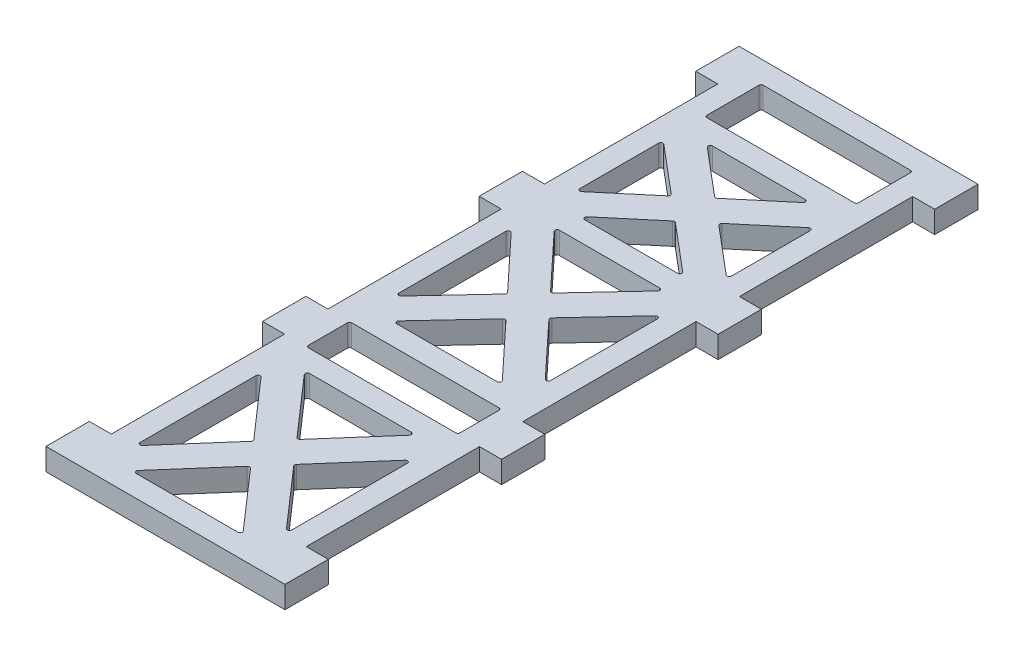
SolidWorks part; units mm, degrees
ref_plane "Front Plane" through (0, 0, 0) normal (0, 0, 1) x (1, 0, 0)
ref_plane "Top Plane" through (0, 0, 0) normal (0, 1, 0) x (1, 0, 0)
ref_plane "Right Plane" through (0, 0, 0) normal (1, 0, 0) x (0, 0, -1)
sketch "Sketch1" plane through (0, 0, 0) normal (0, 1, 0) x (1, 0, 0)
  line L1 (22.5, -80) -> (-22.5, -80)
  line L2 (22.5, -80) -> (22.5, 80)
  line L3 (22.5, 80) -> (-22.5, 80)
  line L4 (-22.5, -80) -> (-22.5, 80)
  line L5 (22.5, -80) -> (-22.5, 80) construction
  line L6 (22.5, 80) -> (-22.5, -80) construction
  point P0 (0, 0)
  dimension "D1" = 45
  dimension "D2" = 160
extrude "Boss-Extrude1" add sketch "Sketch1" along normal blind 5.08
sketch "Sketch2" plane through (0, 5.08, 0) normal (0, 1, 0) x (1, 0, 0)
  line L0 (22.5, 30) -> (27.58, 30)
  line L1 (22.5, 80) -> (27.58, 80)
  line L2 (22.5, 80) -> (22.5, 70)
  line L3 (22.5, 70) -> (27.58, 70)
  line L4 (27.58, 80) -> (27.58, 70)
  line L5 (22.5, 30) -> (22.5, 20)
  line L6 (22.5, 20) -> (27.58, 20)
  line L7 (27.58, 30) -> (27.58, 20)
  line L8 (22.5, -20) -> (27.58, -20)
  line L9 (22.5, -20) -> (22.5, -30)
  line L10 (22.5, -30) -> (27.58, -30)
  line L11 (27.58, -20) -> (27.58, -30)
  line L12 (22.5, -70) -> (27.58, -70)
  line L13 (22.5, -70) -> (22.5, -80)
  line L14 (22.5, -80) -> (27.58, -80)
  line L15 (27.58, -70) -> (27.58, -80)
  line L16 (22.5, -80) -> (22.5, 80) construction
  line L18 (-22.5, -80) -> (22.5, -80) construction
  dimension "D1" = 10
  dimension "D2" = 5.08
  dimension "D3" = 4
extrude "Boss-Extrude2" add sketch "Sketch2" against normal up to surface (5.08 mm away) up to face at (0, 0, 0)
mirror "Mirror1" about plane through (0, 0, 0) normal (1, 0, 0) of "Boss-Extrude2"
sketch "Sketch3" plane through (0, 5.08, 0) normal (0, 1, 0) x (1, 0, 0)
  line L0 (27.58, 80) -> (-27.58, 80) construction
  line L1 (17.5, 62) -> (-17.5, 62)
  line L2 (17.5, 62) -> (17.5, 75)
  line L3 (17.5, 75) -> (-17.5, 75)
  line L4 (-17.5, 62) -> (-17.5, 75)
  line L5 (17.5, 62) -> (-17.5, 75) construction
  line L6 (17.5, 75) -> (-17.5, 62) construction
  line L7 (17.5, 75) -> (22.5, 75) construction
  line L8 (17.5, 75) -> (17.5, 80) construction
  line L9 (17.5, 80) -> (22.5, 80) construction
  line L10 (22.5, 75) -> (22.5, 80) construction
  line L11 (22.5, 30) -> (22.5, 70) construction
  line L12 (-17.5, 27.5) -> (17.5, 57) construction
  line L13 (-17.5, 57) -> (17.5, 57)
  line L14 (-17.5, 57) -> (-17.5, 27.5)
  line L15 (-17.5, 27.5) -> (17.5, 27.5)
  line L16 (17.5, 57) -> (17.5, 27.5)
  line L17 (17.5, 27.5) -> (-17.5, 57) construction
  line L18 (-27.58, -80) -> (27.58, -80) construction
  line L19 (-17.5, 22.5) -> (17.5, 22.5)
  line L20 (-17.5, 22.5) -> (-17.5, -15)
  line L21 (-17.5, -15) -> (17.5, -15)
  line L22 (17.5, 22.5) -> (17.5, -15)
  line L23 (-17.5, -20) -> (17.5, -20)
  line L24 (-17.5, -20) -> (-17.5, -30)
  line L25 (-17.5, -30) -> (17.5, -30)
  line L26 (17.5, -20) -> (17.5, -30)
  line L27 (-17.5, -35) -> (17.5, -35)
  line L28 (-17.5, -35) -> (-17.5, -75)
  line L29 (-17.5, -75) -> (17.5, -75)
  line L30 (17.5, -35) -> (17.5, -75)
  line L31 (-17.5, -75) -> (-22.5, -75) construction
  line L32 (-17.5, -75) -> (-17.5, -80) construction
  line L33 (-17.5, -80) -> (-22.5, -80) construction
  line L34 (-22.5, -75) -> (-22.5, -80) construction
  line L35 (17.5, -75) -> (-17.5, -35) construction
  line L36 (-17.5, -30) -> (17.5, -20) construction
  line L37 (-17.5, -15) -> (17.5, 22.5) construction
  line L38 (17.5, 57) -> (17.5, 62) construction
  line L39 (17.5, 27.5) -> (17.5, 22.5) construction
  line L40 (27.58, -20) -> (22.5, -20) construction
  line L41 (17.5, -30) -> (17.5, -35) construction
  line L42 (-27.58, -25) -> (27.58, -25) construction
  line L43 (-27.58, -30) -> (-27.58, -20) construction
  line L44 (27.58, -30) -> (27.58, -20) construction
  line L45 (27.58, 25) -> (-27.58, 25) construction
  line L46 (27.58, 20) -> (27.58, 30) construction
  line L47 (-27.58, 20) -> (-27.58, 30) construction
  point P0 (0, 68.5)
  point P17 (0, 42.25)
  point P35 (0, 3.75)
  point P36 (0, -55)
  point P37 (0, -25)
  point P52 (17.5, 25)
  dimension "D1" = 5
  dimension "D2" = 13
  dimension "D3" = 5
extrude "Cut-Extrude1" cut sketch "Sketch3" against normal through all
sketch "Sketch4" plane through (0, 5.08, 0) normal (0, 1, 0) x (1, 0, 0)
  line L0 (-17.5, -75) -> (17.5, -35) construction
  line L1 (17.5, -75) -> (-17.5, -35) construction
  line L2 (-17.5, -40.3151) -> (-4.6507, -55)
  line L3 (-17.5, -35) -> (-17.5, -75) construction
  line L4 (-4.6507, -55) -> (-17.5, -69.6849)
  line L5 (-17.5, -69.6849) -> (-17.5, -75)
  line L6 (-17.5, -75) -> (-12.8493, -75)
  line L7 (-17.5, -75) -> (17.5, -75) construction
  line L8 (-12.8493, -75) -> (0, -60.3151)
  line L9 (0, -60.3151) -> (12.8493, -75)
  line L10 (12.8493, -75) -> (17.5, -75)
  line L11 (17.5, -75) -> (17.5, -69.6849)
  line L12 (17.5, -75) -> (17.5, -35) construction
  line L13 (17.5, -69.6849) -> (4.6507, -55)
  line L14 (4.6507, -55) -> (17.5, -40.3151)
  line L15 (17.5, -40.3151) -> (17.5, -35)
  line L16 (17.5, -35) -> (12.8493, -35)
  line L17 (17.5, -35) -> (-17.5, -35) construction
  line L18 (12.8493, -35) -> (0, -49.6849)
  line L19 (0, -49.6849) -> (-12.8493, -35)
  line L20 (-12.8493, -35) -> (-17.5, -35)
  line L21 (-17.5, -35) -> (-17.5, -40.3151)
  line L22 (-17.5, -15) -> (17.5, 22.5) construction
  line L23 (17.5, -15) -> (-17.5, 22.5) construction
  line L24 (-17.5, 27.5) -> (17.5, 57) construction
  line L25 (17.5, 27.5) -> (-17.5, 57) construction
  line L26 (-12.7124, 22.5) -> (0, 8.8796)
  line L27 (17.5, 22.5) -> (-17.5, 22.5) construction
  line L28 (0, 8.8796) -> (12.7124, 22.5)
  line L29 (12.7124, 22.5) -> (17.5, 22.5)
  line L30 (17.5, 22.5) -> (17.5, 17.3704)
  line L31 (17.5, -15) -> (17.5, 22.5) construction
  line L32 (17.5, 17.3704) -> (4.7876, 3.75)
  line L33 (4.7876, 3.75) -> (17.5, -9.8704)
  line L34 (17.5, -9.8704) -> (17.5, -15)
  line L35 (17.5, -15) -> (12.7124, -15)
  line L36 (-17.5, -15) -> (17.5, -15) construction
  line L37 (12.7124, -15) -> (0, -1.3796)
  line L38 (0, -1.3796) -> (-12.7124, -15)
  line L39 (-12.7124, -15) -> (-17.5, -15)
  line L40 (-17.5, -15) -> (-17.5, -9.8704)
  line L41 (-17.5, 22.5) -> (-17.5, -15) construction
  line L42 (-17.5, -9.8704) -> (-4.7876, 3.75)
  line L43 (-4.7876, 3.75) -> (-17.5, 17.3704)
  line L44 (-17.5, 17.3704) -> (-17.5, 22.5)
  line L45 (-17.5, 22.5) -> (-12.7124, 22.5)
  line L46 (-17.5, 52.4226) -> (-5.4308, 42.25)
  line L47 (-17.5, 57) -> (-17.5, 27.5) construction
  line L48 (-5.4308, 42.25) -> (-17.5, 32.0774)
  line L49 (-17.5, 32.0774) -> (-17.5, 27.5)
  line L50 (-17.5, 27.5) -> (-12.0692, 27.5)
  line L51 (-17.5, 27.5) -> (17.5, 27.5) construction
  line L52 (-12.0692, 27.5) -> (0, 37.6726)
  line L53 (0, 37.6726) -> (12.0692, 27.5)
  line L54 (12.0692, 27.5) -> (17.5, 27.5)
  line L55 (17.5, 27.5) -> (17.5, 32.0774)
  line L56 (17.5, 27.5) -> (17.5, 57) construction
  line L57 (17.5, 32.0774) -> (5.4308, 42.25)
  line L58 (5.4308, 42.25) -> (17.5, 52.4226)
  line L59 (17.5, 52.4226) -> (17.5, 57)
  line L60 (17.5, 57) -> (12.0692, 57)
  line L61 (12.0692, 57) -> (0, 46.8274)
  line L62 (0, 46.8274) -> (-12.0692, 57)
  line L63 (17.5, 57) -> (-17.5, 57) construction
  line L64 (-12.0692, 57) -> (-17.5, 57)
  line L65 (-17.5, 57) -> (-17.5, 52.4226)
  point P22 (0, -55)
  point P45 (0, 42.25)
  point P46 (0, 3.75)
  dimension "D1" = 7
  dimension "D2" = 7
  dimension "D3" = 7
extrude "Boss-Extrude3" add sketch "Sketch4" against normal up to surface (5.08 mm away) up to face at (0, 0, 55)
fillet "Fillet1" radius 0.5 44 edges at (17.5, 2.54, -75) (-17.5, 2.54, -75) (-17.5, 2.54, -62) (17.5, 2.54, -62) (17.5, 2.54, 20) (17.5, 2.54, 30) (-17.5, 2.54, 30) (-17.5, 2.54, 20) (4.6507, 2.54, 55) (17.5, 2.54, 40.3151) (17.5, 2.54, 69.6849) (12.8493, 2.54, 75) (0, 2.54, 60.3151) (-12.8493, 2.54, 75) (-17.5, 2.54, 69.6849) (-4.6507, 2.54, 55) (-17.5, 2.54, 40.3151) (0, 2.54, 49.6849) (12.8493, 2.54, 35) (-12.8493, 2.54, 35) (-17.5, 2.54, -17.3704) (-4.7876, 2.54, -3.75) (-17.5, 2.54, 9.8704) (-12.7124, 2.54, 15) (0, 2.54, 1.3796) (12.7124, 2.54, 15) (17.5, 2.54, 9.8704) (17.5, 2.54, -17.3704) (4.7876, 2.54, -3.75) (12.7124, 2.54, -22.5) (0, 2.54, -8.8796) (-12.7124, 2.54, -22.5) (-17.5, 2.54, -52.4226) (-5.4308, 2.54, -42.25) (-17.5, 2.54, -32.0774) (-12.0692, 2.54, -27.5) (0, 2.54, -37.6726) (12.0692, 2.54, -27.5) (5.4308, 2.54, -42.25) (17.5, 2.54, -32.0774) (17.5, 2.54, -52.4226) (0, 2.54, -46.8274) (12.0692, 2.54, -57) (-12.0692, 2.54, -57)
